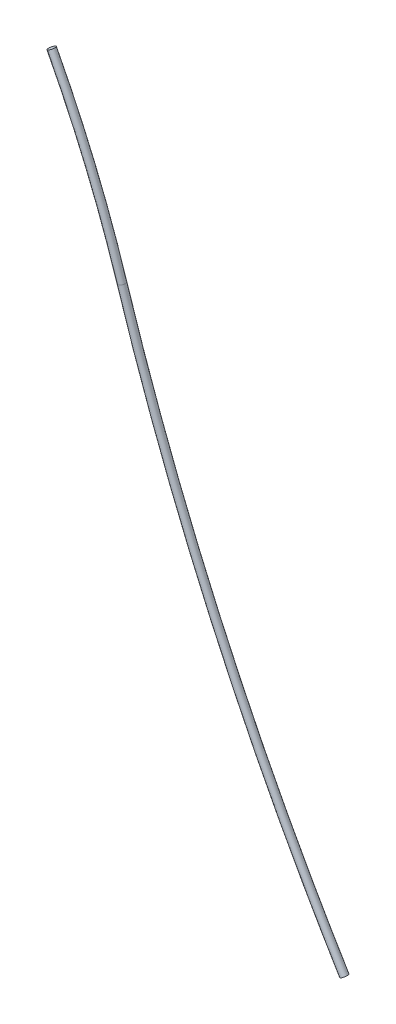
SolidWorks part; units mm, degrees
ref_plane "Plano frontal" through (0, 0, 0) normal (0, 0, 1) x (1, 0, 0)
ref_plane "Plano superior" through (0, 0, 0) normal (0, 1, 0) x (1, 0, 0)
ref_plane "Plano direito" through (0, 0, 0) normal (1, 0, 0) x (0, 0, -1)
sketch "Esboço1" plane through (0, 0, 0) normal (0, 0, 1) x (1, 0, 0)
  arc A0 (-59.1206, 114.2739) -> (-39.1606, 66.5285) centre (-323.7374, -24.394) cw
  arc A1 (-39.1606, 66.5285) -> (23.9342, -72.171) centre (579.0037, 264.0323) ccw
sweep "Varredura1" add path "Esboço1" circular profile diameter 2 parameters "D3"=2
